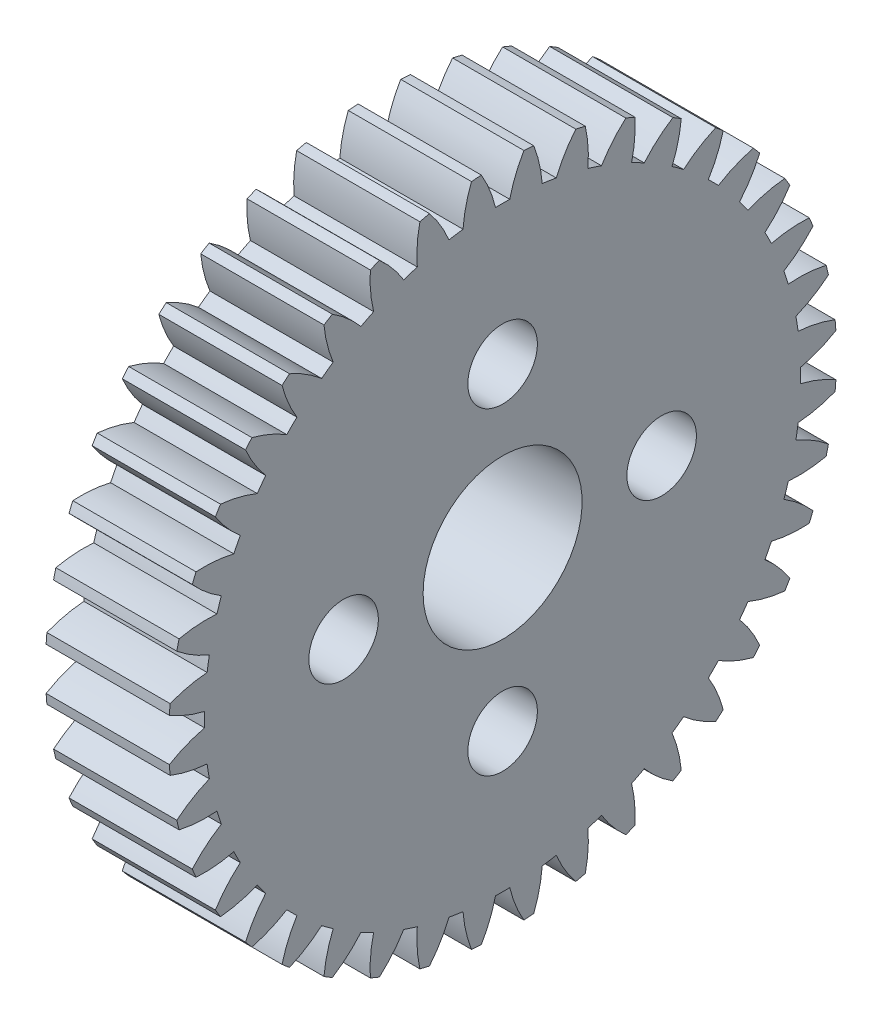
SolidWorks part; units mm, degrees
material "6061 Alloy"
ref_plane "Plane1" through (0, 0, 0) normal (0, 0, 1) x (1, 0, 0)
ref_plane "Plane2" through (0, 0, 0) normal (0, 1, 0) x (1, 0, 0)
ref_plane "Plane3" through (0, 0, 0) normal (1, 0, 0) x (0, 0, -1)
sketch "HoldingSke" plane through (0, 0, 0) normal (0, 1, 0) x (1, 0, 0)
  line L0 (0, 0) -> (0.9576, -0.8035)
  line L1 (-15, 0) -> (100, 0) construction
  line L2 (0, 0) -> (-2.1039, 2.3779)
  line L3 (0, 0) -> (-11.863, 4.5341)
  line L4 (0, 0) -> (6.6156, 5.5511)
  line L5 (0, 0) -> (-46.8476, -17.4728)
  line L6 (0, 0) -> (-5.1396, -3.4677)
  line L7 (-2.1039, 2.3779) -> (8.6586, 51.2059)
  line L8 (-76.2, 54.61) -> (-74.8, 54.61)
  line L9 (-71.009, 38.7566) -> (-53.1078, 45.2721)
  line L10 (-76.2, 71.12) -> (104.1128, 71.12)
  line L11 (0, 0) -> (-6.2, 0)
  line L12 (-76.2, 101.6) -> (-76.17, 101.6)
  line L13 (24.9733, 27.94) -> (52.9518, 28.4284)
  line L14 (24.9733, 27.94) -> (24.9743, 27.94)
  line L15 (24.9733, 27.94) -> (100.4006, 29.5858)
  line L16 (-63.627, -0.8) -> (-12.827, -0.8)
  circle A0 centre (0, 0) radius 4
  circle A1 centre (0, 0) radius 14.999
  circle A2 centre (0, 0) radius 37.5
  circle A3 centre (0, 0) radius 4
  dimension "MHD" = 29.998
  dimension "Hub_dia" = 75
  dimension "Bore" = 8
  dimension "MBD" = 8
  dimension "Num_teeth" = 40
  dimension "Pitch_radius" = 180.3128
  dimension "Pitch" = 1.25
  dimension "Width" = 6.2
  dimension "Overall_len" = 50
  dimension "Show_teeth" = 40
  dimension "Thickness" = 6.2
  dimension "OAL" = 50.0001
  dimension "T_dim" = 1.4
  dimension "Ap" = 20
  dimension "H" = 19.05
  dimension "Backlash" = 0.03
  dimension "Addendum_fac" = 1
  dimension "Dedendum_fac" = 1.25
  dimension "Clearance_fac" = 0.25
  dimension "Dedendum_add" = 0.001
  dimension "Module" = 0.8
sketch "BasProSke" plane through (0, 0, 0) normal (0, 1, 0) x (1, 0, 0)
  line L0 (-10, 0) -> (60, 0) construction
  line L1 (0, 0) -> (0, 16.8)
  line L2 (0, 0) -> (6.2, 0)
  line L3 (6.2, 0) -> (6.2, 16.8)
  line L4 (6.2, 16.8) -> (0, 16.8)
  dimension "Diameter" = 33.6
  dimension "Thickness" = 6.2
revolve "Base-Revolve" add sketch "BasProSke" angle 360 about L0
sketch "TooCutSke" plane through (0, 0, 0) normal (1, 0, 0) x (0, 0, -1)
  line L1 (0, 0) -> (0, 107) construction
  line L2 (0, 0) -> (-0.6807, 15.9855) construction
  line L3 (0, 0) -> (-2.5091, 31.8807) construction
  line L4 (-0.6807, 15.9855) -> (-1.2545, 15.9404) construction
  arc A0 (0.3582, 14.9947) -> (-0.3582, 14.9947) centre (0, 0) ccw
  arc A1 (1.086, 16.7903) -> (-1.086, 16.7903) centre (0, 0) ccw
  circle A2 centre (0, 0) radius 16 construction
  circle A3 centre (0, 0) radius 15.0351 construction
  arc A4 (-0.3582, 14.9947) -> (-1.086, 16.7903) centre (-6.5851, 13.5163) ccw
  arc A5 (1.086, 16.7903) -> (0.3582, 14.9947) centre (6.5851, 13.5163) ccw
  dimension "Root_dia" = 29.998
  dimension "Overcut_dia" = 33.6508
  dimension "Pitch_dia" = 32
  dimension "Base_dia" = 30.0702
  dimension "Flank_rad" = 6.4
  dimension "Half_ang" = 4.5
  dimension "Half_CT" = 0.5757
extrude "ToothCut" cut sketch "TooCutSke" along normal through all
fillet "Breaks" [suppressed] radius 0.016
fillet "RootFillets" [suppressed] radius 0.201
pattern_circular "TeethCuts" count 40 every 9 about axis through (-10, 0, 0) along (1, 0, 0) of "ToothCut", "RootFillets", "Breaks"
sketch "HubNeaOneSke" plane through (0, 0, 0) normal (-1, 0, 0) x (0, 0, 1)
  circle A0 centre (0, 0) radius 14.999
  dimension "Diameter" = 29.998
extrude "HubNearOne" [suppressed] add sketch "HubNeaOneSke" along normal blind 43.8001
sketch "HubNeaBotSke" plane through (0, 0, 0) normal (-1, 0, 0) x (0, 0, 1)
  circle A0 centre (0, 0) radius 14.999
  dimension "Diameter" = 29.998
extrude "HubNearBoth" [suppressed] add sketch "HubNeaBotSke" along normal blind 21.9
ref_plane "FarPln" through (6.2, 0, 0) normal (1, 0, 0) x (0, 0, -1)
sketch "HubFarSke" plane through (6.2, 0, 0) normal (1, 0, 0) x (0, 0, -1)
  circle A0 centre (0, 0) radius 14.999
  dimension "Diameter" = 29.998
extrude "HubFar" [suppressed] add sketch "HubFarSke" along normal blind 21.9
sketch "BorSke" plane through (0, 0, 0) normal (1, 0, 0) x (0, 0, -1)
  circle A0 centre (0, 0) radius 4
  dimension "Diameter" = 8
extrude "Bore" cut sketch "BorSke" along normal mid plane 100.0001
sketch "KeySke" plane through (0, 0, 0) normal (1, 0, 0) x (0, 0, -1)
  line L0 (-1.5, 0) -> (-1.5, 5.4)
  line L1 (-1.5, 5.4) -> (1.5, 5.4)
  line L2 (1.5, 5.4) -> (1.5, 0)
  line L3 (0, 0) -> (0, 34) construction
  line L4 (-1.5, 0) -> (1.5, 0)
  dimension "Offset" = 5.4
  dimension "Width" = 3
extrude "Keyway" [suppressed] cut sketch "KeySke" along normal mid plane 100.0001
pattern_circular "Keyway2" [suppressed] count 2 every 90 about axis through (-10, 0, 0) along (1, 0, 0)
sketch "Sketch1" plane through (6.2, 0, 0) normal (1, 0, 0) x (0, 0, -1)
  line L0 (-8, 0) -> (8, 0) construction
  line L1 (0, 8) -> (0, -8) construction
  circle A0 centre (0, 8) radius 1.75
  circle A1 centre (0, -8) radius 1.75
  circle A2 centre (8, 0) radius 1.75
  circle A3 centre (-8, 0) radius 1.75
  circle A4 centre (0, 0) radius 8 construction
  dimension "D1" = 3.5
  dimension "D2" = 16
hole_wizard "Ø3.5 (3.5) Diameter Hole1" positions "Sketch3" profile "Sketch2" hole size "Ø3.5" standard "Ansi Metric" end condition through all
sketch "Sketch3" plane through (6.2, 0, 0) normal (1, 0, 0) x (0, 0, -1)
  point P0 (0, 8)
  point P1 (8, 0)
  point P4 (0, -8)
  point P7 (-8, 0)
sketch "Sketch2" plane through (6.2, 8, 0) normal (0, 1, 0) x (0, 0, -1)
  line L0 (0, 0) -> (0, 6.2)
  line L1 (0, 6.2) -> (1.75, 6.2)
  line L2 (1.75, 6.2) -> (1.75, 0)
  line L5 (1.75, 0) -> (0, 0)
  line L11 (0, -6.35) -> (0, 107.95) construction
  dimension "Thru Hole Dia." = 3.5
  dimension "Thru Hole Depth" = 6.2
equation "' \"Module@HoldingSke\" = 6.35"
equation "' \"Num_teeth@HoldingSke\" = 12"
equation "' \"Ap@HoldingSke\" =  20"
equation "' \"Width@HoldingSke\" = 0.5 * 25.4"
equation "' \"Hub_dia@HoldingSke\"= 1 * 25.4"
equation "' \"Overall_len@HoldingSke\" = 1.0 * 25.4"
equation "' \"Bore@HoldingSke\" = 0.75 * 25.4"
equation "' \"T_dim@HoldingSke\" = 0.1 * 25.4"
equation "' \"Width@KeySke\" = 0.25 * 25.4"
equation "' \"Show_teeth@HoldingSke\" = 13"
equation "' \"Backlash@HoldingSke\" = 0.009 * 25.4"
equation "' \"Addendum_fac@HoldingSke\" = 1.0"
equation "' \"Dedendum_fac@HoldingSke\" = 1.25"
equation "' \"Dedendum_add@HoldingSke\" = 0.00005 * 25.4"
equation "' \"Clearance_fac@HoldingSke\" = 0.25"
equation "\"Pitch@HoldingSke\" = 1 / \"Module@HoldingSke\""
equation "\"Overcut_dia@TooCutSke\" = (\"Num_teeth@HoldingSke\" + 2 * \"Addendum_fac@HoldingSke\") / \"Pitch@HoldingSke\" + 0.002 * 25.4"
equation "\"Pitch_dia@TooCutSke\" = \"Num_teeth@HoldingSke\" / \"Pitch@HoldingSke\""
equation "\"Base_dia@TooCutSke\" = \"Num_teeth@HoldingSke\" / \"Pitch@HoldingSke\" * cos((\"Ap@HoldingSke\"  * 3.14159265 / 180))"
equation "\"Root_dia@TooCutSke\" = (\"Num_teeth@HoldingSke\" + 2) / \"Pitch@HoldingSke\" - 2 * (\"Addendum_fac@HoldingSke\" + \"Dedendum_fac@HoldingSke\") / \"Pitch@HoldingSke\" - \"Dedendum_add@HoldingSke\" * 2"
equation "\"Half_ang@TooCutSke\" = 180 / \"Num_teeth@HoldingSke\""
equation "\"Half_CT@TooCutSke\" = \"Num_teeth@HoldingSke\" / \"Pitch@HoldingSke\" * sin((3.14159265 / 2 / \"Num_teeth@HoldingSke\")) / 2 - 7 * \"Backlash@HoldingSke\" / 4"
equation "\"Flank_rad@TooCutSke\" = \"Num_teeth@HoldingSke\" / \"Pitch@HoldingSke\" / 5"
equation "\"Radius@RootFillets\" = \"Clearance_fac@HoldingSke\" / \"Pitch@HoldingSke\" + \"Dedendum_add@HoldingSke\""
equation "\"Break_rad@Breaks\" = 0.02 / \"Pitch@HoldingSke\""
equation "\"Thickness@HoldingSke\" = \"Width@HoldingSke\""
equation "\"OAL@HoldingSke\" = \"Thickness@HoldingSke\""
equation "\"MHD@HoldingSke\" = (\"Num_teeth@HoldingSke\" + 2) / \"Pitch@HoldingSke\" - 2 * (\"Addendum_fac@HoldingSke\" + \"Dedendum_fac@HoldingSke\")  / \"Pitch@HoldingSke\" - \"Dedendum_add@HoldingSke\" * 2"
equation "\"MBD@HoldingSke\" = (\"Num_teeth@HoldingSke\" + 2) / \"Pitch@HoldingSke\" - 2 * (\"Addendum_fac@HoldingSke\" + \"Dedendum_fac@HoldingSke\")  / \"Pitch@HoldingSke\" - \"Dedendum_add@HoldingSke\" * 2 - 0.002 * 25.4"
equation "\"MHD@HoldingSke\" = ((sgn( \"MHD@HoldingSke\" - \"Hub_dia@HoldingSke\" )-1)*( \"MHD@HoldingSke\" - \"Hub_dia@HoldingSke\" ))/-2+ \"Hub_dia@HoldingSke\""
equation "\"MBD@HoldingSke\" = ((sgn( \"MBD@HoldingSke\" - \"Bore@HoldingSke\" )-1)*( \"MBD@HoldingSke\" - \"Bore@HoldingSke\" ))/-2+ \"Bore@HoldingSke\""
equation "\"OAL@HoldingSke\" = ((sgn( \"OAL@HoldingSke\" - \"Overall_len@HoldingSke\" )+1)*( \"OAL@HoldingSke\" - \"Overall_len@HoldingSke\" ))/2 + \"Overall_len@HoldingSke\" + 0.000002 * 25.4"
equation "\"Num_teeth@TeethCuts\" = int( \"Show_teeth@HoldingSke\" ) + 1"
equation "\"Num_teeth@TeethCuts\" = ((sgn( \"Num_teeth@TeethCuts\" - \"Num_teeth@HoldingSke\" )-1)*( \"Num_teeth@TeethCuts\" - \"Num_teeth@HoldingSke\" ))/-2+ \"Num_teeth@HoldingSke\""
equation "\"Num_teeth@TeethCuts\" = ((sgn( \"Num_teeth@TeethCuts\" - 2.0)+1)*( \"Num_teeth@TeethCuts\" - 2.0))/2 +2.0"
equation "\"Angle@TeethCuts\" = 360.0 / \"Num_teeth@HoldingSke\""
equation "\"Diameter@BasProSke\" = (\"Num_teeth@HoldingSke\" + 2 * \"Addendum_fac@HoldingSke\") / \"Pitch@HoldingSke\""
equation "\"Thickness@BasProSke\"  = \"Thickness@HoldingSke\""
equation "' \"Fillet_rad@BasProSke\" =  \"Thickness@HoldingSke\" * 0.05"
equation "\"MHD@HoldingSke\" = ((sgn( \"MHD@HoldingSke\" - \"Root_dia@TooCutSke\" )-1)*( \"MHD@HoldingSke\" - \"Root_dia@TooCutSke\" ))/-2+ \"Root_dia@TooCutSke\""
equation "\"Diameter@HubNeaOneSke\" = \"MHD@HoldingSke\""
equation "\"Length@HubNearOne\" = \"OAL@HoldingSke\" - \"Thickness@BasProSke\""
equation "\"Diameter@HubNeaBotSke\" = \"MHD@HoldingSke\""
equation "\"Length@HubNearBoth\" = ( \"OAL@HoldingSke\" - \"Thickness@BasProSke\" ) / 2.0"
equation "\"Thickness@FarPln\" = \"Thickness@BasProSke\""
equation "\"Diameter@HubFarSke\" = \"MHD@HoldingSke\""
equation "\"Length@HubFar\" = ( \"OAL@HoldingSke\" - \"Thickness@BasProSke\" ) / 2.0"
equation "\"Diameter@BorSke\" = \"MBD@HoldingSke\""
equation "\"D1@Bore\" = \"OAL@HoldingSke\" * 2.0"
equation "\"D1@Keyway\" = \"OAL@HoldingSke\" * 2.0"
equation "\"Offset@KeySke\" = \"T_dim@HoldingSke\" + \"MBD@HoldingSke\" / 2.0"
